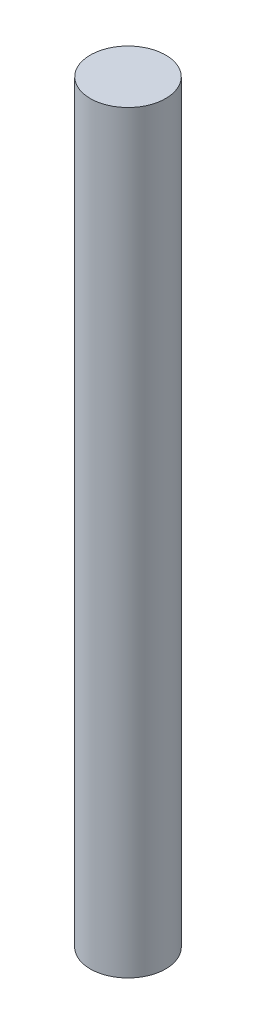
SolidWorks part; units mm, degrees
ref_plane "Front Plane" through (0, 0, 0) normal (0, 0, 1) x (1, 0, 0)
ref_plane "Top Plane" through (0, 0, 0) normal (0, 1, 0) x (1, 0, 0)
ref_plane "Right Plane" through (0, 0, 0) normal (1, 0, 0) x (0, 0, -1)
sketch "Sketch5" plane through (0, 0, 0) normal (0, 1, 0) x (1, 0, 0)
  circle A0 centre (0, 0) radius 3
  dimension "D1" = 6
extrude "Boss-Extrude3" add sketch "Sketch5" along normal blind 60
